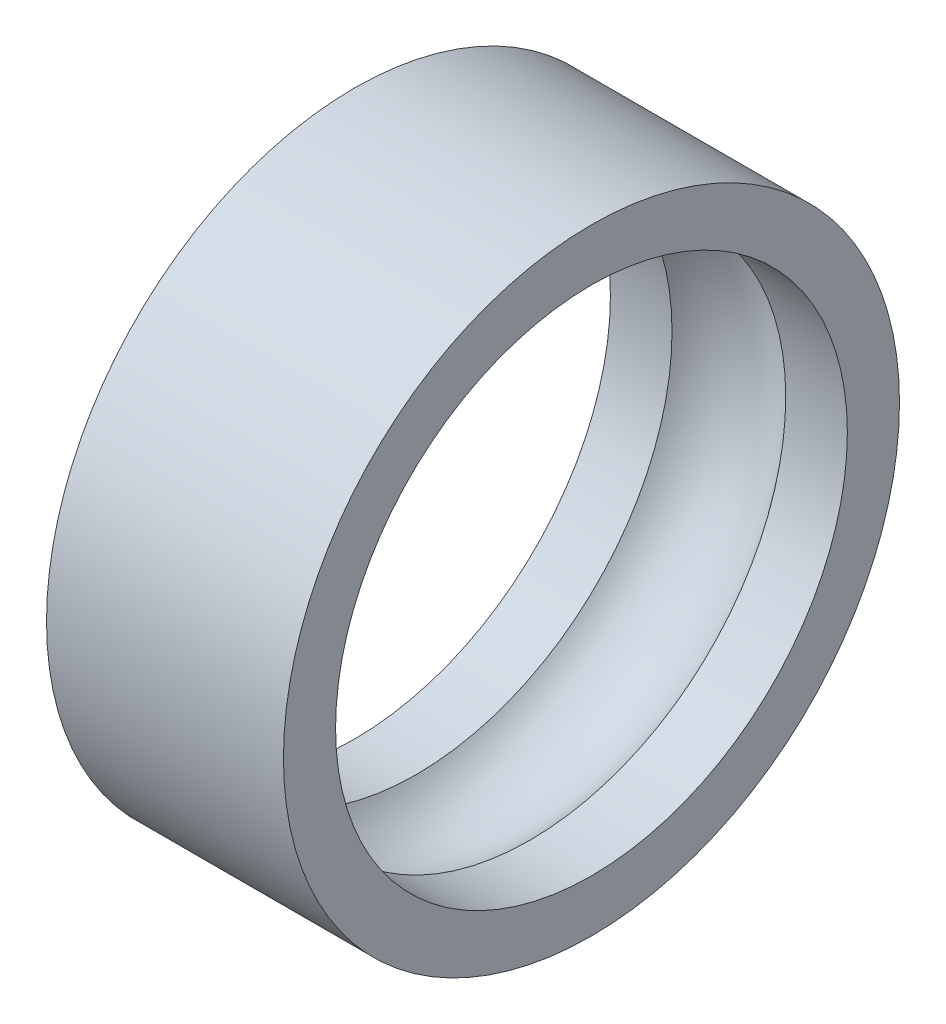
SolidWorks part; units mm, degrees
ref_plane "Ön Düzlem" through (0, 0, 0) normal (0, 0, 1) x (1, 0, 0)
ref_plane "Üst Düzlem" through (0, 0, 0) normal (0, 1, 0) x (1, 0, 0)
ref_plane "Sağ Düzlem" through (0, 0, 0) normal (1, 0, 0) x (0, 0, -1)
sketch "Çizim2" plane through (0, 0, 0) normal (0, 0, 1) x (1, 0, 0)
  line L0 (-2.5, 6.5) -> (2.5, 6.5)
  line L1 (2.5, 6.5) -> (2.5, 5.4)
  line L2 (2.5, 5.4) -> (1.2, 5.4)
  line L3 (-2.5, 5.4) -> (-2.5, 6.5)
  line L4 (-1.2, 5.4) -> (-2.5, 5.4)
  line L5 (0, 0) -> (-24.2609, 0) construction
  arc A0 (1.2, 5.4) -> (-1.2, 5.4) centre (0, 4.5) ccw
  point P0 (0, 6.5)
  point P9 (0, 6)
  dimension "D1" = 6.5
  dimension "D2" = 1.1
  dimension "D3" = 5
  dimension "D4" = 0.6
  dimension "D5" = 1.5
revolve "Döndür1" add sketch "Çizim2" angle 360 about L5
